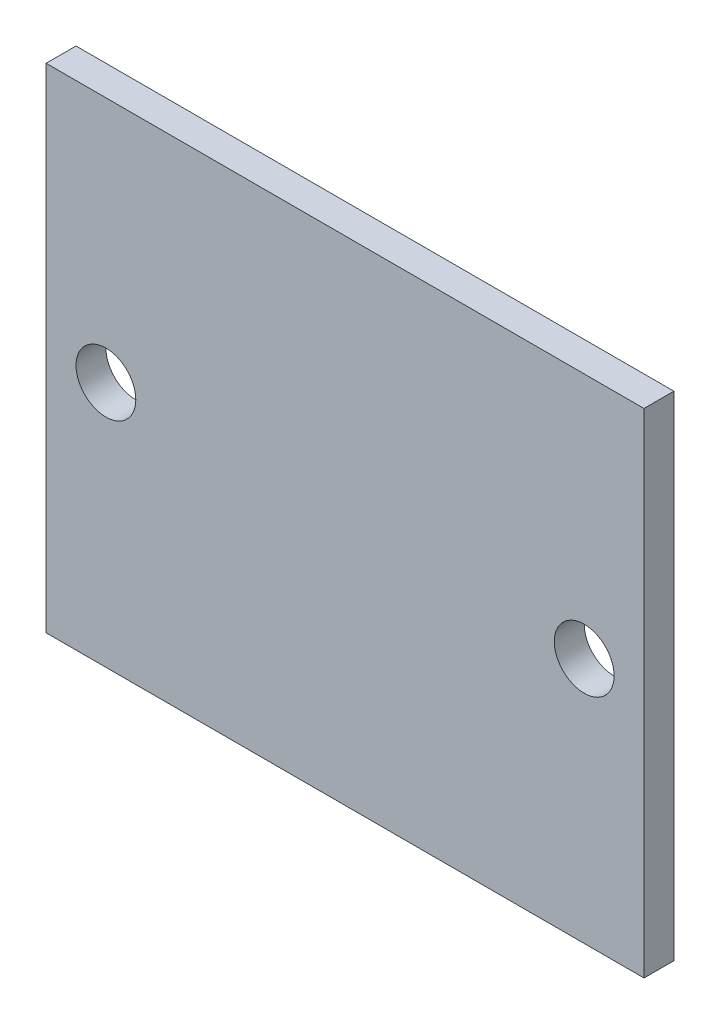
SolidWorks part; units mm, degrees
ref_plane "Ebene vorne" through (0, 0, 0) normal (0, 0, 1) x (1, 0, 0)
ref_plane "Ebene oben" through (0, 0, 0) normal (0, 1, 0) x (1, 0, 0)
ref_plane "Ebene rechts" through (0, 0, 0) normal (1, 0, 0) x (0, 0, -1)
sketch "Skizze1" plane through (0, 0, 0) normal (0, 0, 1) x (1, 0, 0)
  line L1 (-10, 8.25) -> (10, 8.25)
  line L2 (-10, 8.25) -> (-10, -8.25)
  line L3 (-10, -8.25) -> (10, -8.25)
  line L4 (10, 8.25) -> (10, -8.25)
  dimension "D1" = 16.5
  dimension "D2" = 8.25
  dimension "D3" = 20
  dimension "D4" = 10
extrude "Aufsatz-Linear austragen1" add sketch "Skizze1" along normal blind 1
sketch "Skizze2" plane through (0, 0, 1) normal (0, 0, 1) x (1, 0, 0)
  line L0 (-10, 8.25) -> (-10, -8.25) construction
  line L1 (10, -8.25) -> (10, 8.25) construction
  line L2 (10, 8.25) -> (-10, 8.25) construction
  circle A0 centre (-8, 0) radius 1
  circle A1 centre (8, 0) radius 1
  point P4 (-10, 0)
  point P7 (10, 0)
  dimension "D1" = 2
  dimension "D2" = 2
  dimension "D3" = 2
  dimension "D4" = 2
  dimension "D5" = 8.25
  dimension "D6" = 8.25
extrude "Schnitt-Linear austragen1" cut sketch "Skizze2" against normal through all
